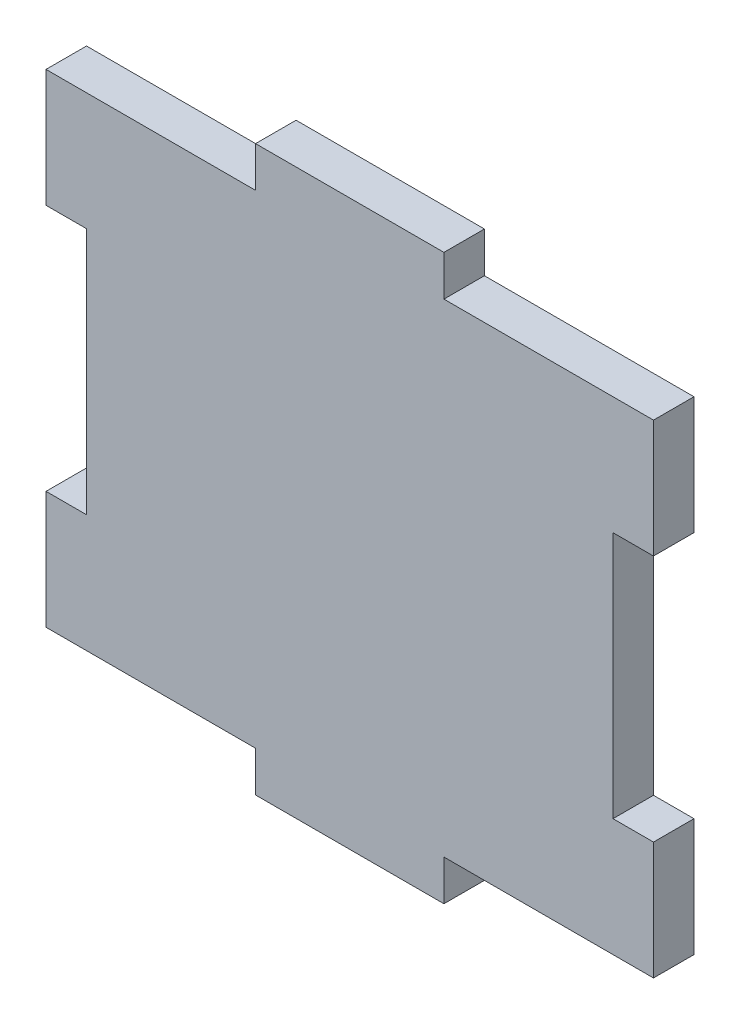
SolidWorks part; units mm, degrees
ref_plane "Front Plane" through (0, 0, 0) normal (0, 0, 1) x (1, 0, 0)
ref_plane "Top Plane" through (0, 0, 0) normal (0, 1, 0) x (1, 0, 0)
ref_plane "Right Plane" through (0, 0, 0) normal (1, 0, 0) x (0, 0, -1)
sketch "Sketch1" plane through (0, 0, 0) normal (0, 0, 1) x (1, 0, 0)
  line L1 (-40.9575, 32.5755) -> (40.9575, 32.5755)
  line L2 (-40.9575, 32.5755) -> (-40.9575, -32.5755)
  line L3 (-40.9575, -32.5755) -> (40.9575, -32.5755)
  line L4 (40.9575, 32.5755) -> (40.9575, -32.5755)
  line L5 (-40.9575, 32.5755) -> (40.9575, -32.5755) construction
  line L6 (-40.9575, -32.5755) -> (40.9575, 32.5755) construction
  point P0 (0, 0)
  dimension "D1" = 65.151
  dimension "D2" = 81.915
extrude "Boss-Extrude1" add sketch "Sketch1" along normal blind 5.461
sketch "Sketch2" plane through (0, 0, 5.461) normal (0, 0, 1) x (1, 0, 0)
  line L0 (-40.9575, 32.5755) -> (-40.9575, -32.5755) construction
  line L1 (-35.4965, 16.7005) -> (-40.9575, 16.7005)
  line L2 (-35.4965, 16.7005) -> (-35.4965, -16.7005)
  line L3 (-35.4965, -16.7005) -> (-40.9575, -16.7005)
  line L4 (-40.9575, 16.7005) -> (-40.9575, -16.7005)
  line L5 (-35.4965, 16.7005) -> (-40.9575, -16.7005) construction
  line L6 (-35.4965, -16.7005) -> (-40.9575, 16.7005) construction
  line L7 (40.9575, -32.5755) -> (40.9575, 32.5755) construction
  line L8 (35.4965, 16.7005) -> (40.9575, 16.7005)
  line L9 (35.4965, 16.7005) -> (35.4965, -16.7005)
  line L10 (35.4965, -16.7005) -> (40.9575, -16.7005)
  line L11 (40.9575, 16.7005) -> (40.9575, -16.7005)
  line L12 (35.4965, 16.7005) -> (40.9575, -16.7005) construction
  line L13 (35.4965, -16.7005) -> (40.9575, 16.7005) construction
  line L14 (40.9575, 32.5755) -> (-40.9575, 32.5755) construction
  point P0 (-38.227, 0)
  point P7 (38.227, 0)
  dimension "D1" = 15.875
  dimension "D2" = 5.461
extrude "Cut-Extrude1" cut sketch "Sketch2" against normal through all
sketch "Sketch3" plane through (0, 0, 0) normal (0, 0, 1) x (1, 0, 0)
  line L1 (-6.3509, -30.0355) -> (6.3509, -30.0355)
  line L2 (6.3509, -30.0355) -> (12.7017, -19.0355)
  line L3 (12.7017, -19.0355) -> (6.3509, -8.0355)
  line L4 (6.3509, -8.0355) -> (-6.3509, -8.0355)
  line L5 (-6.3509, -8.0355) -> (-12.7017, -19.0355)
  line L6 (-12.7017, -19.0355) -> (-6.3509, -30.0355)
  line L7 (-40.9575, -32.5755) -> (40.9575, -32.5755) construction
  circle A0 centre (0, -19.0355) radius 7.7
  circle A1 centre (0, -19.0355) radius 11 construction
  dimension "D2" = 15.4
  dimension "D1" = 22
  dimension "D4" = 2.54
extrude "Cut-Extrude2" [suppressed] cut sketch "Sketch3" along normal blind 2.54
sketch "Sketch4" plane through (0, 0, 5.461) normal (0, 0, 1) x (1, 0, 0)
  line L12 (-35.4965, 16.7005) -> (-35.4965, -16.7005)
  line L13 (-35.4965, 16.7005) -> (-35.4965, -16.7005)
  line L14 (-40.9575, 16.7005) -> (-35.4965, 16.7005)
  line L15 (-40.9575, 16.7005) -> (-35.4965, 16.7005)
  line L16 (-40.9575, 32.5755) -> (-40.9575, 16.7005)
  line L17 (-40.9575, 32.5755) -> (-40.9575, 16.7005)
  line L18 (40.9575, 32.5755) -> (-40.9575, 32.5755)
  line L19 (40.9575, 32.5755) -> (-40.9575, 32.5755)
  line L20 (40.9575, 16.7005) -> (40.9575, 32.5755)
  line L21 (40.9575, 16.7005) -> (40.9575, 32.5755)
  line L22 (35.4965, 16.7005) -> (40.9575, 16.7005)
  line L23 (35.4965, 16.7005) -> (40.9575, 16.7005)
  line L24 (35.4965, -16.7005) -> (35.4965, 16.7005)
  line L25 (35.4965, -16.7005) -> (35.4965, 16.7005)
  line L26 (40.9575, -16.7005) -> (35.4965, -16.7005)
  line L27 (40.9575, -16.7005) -> (35.4965, -16.7005)
  line L28 (40.9575, -32.5755) -> (40.9575, -16.7005)
  line L29 (40.9575, -32.5755) -> (40.9575, -16.7005)
  line L30 (-40.9575, -32.5755) -> (40.9575, -32.5755)
  line L31 (-40.9575, -32.5755) -> (40.9575, -32.5755)
  line L32 (-40.9575, -16.7005) -> (-40.9575, -32.5755)
  line L33 (-40.9575, -16.7005) -> (-40.9575, -32.5755)
  line L34 (-35.4965, -16.7005) -> (-40.9575, -16.7005)
  line L35 (-35.4965, -16.7005) -> (-40.9575, -16.7005)
  dimension "D1" = 0
extrude "Cut-Extrude3" [suppressed] cut sketch "Sketch4" against normal through all
sketch "Sketch5" plane through (0, 0, 0) normal (0, 0, -1) x (-1, 0, 0)
  line L0 (-40.9575, 32.5755) -> (40.9575, 32.5755) construction
  line L1 (12.7, 38.0365) -> (-12.7, 38.0365)
  line L2 (12.7, 38.0365) -> (12.7, 32.5755)
  line L3 (12.7, 32.5755) -> (-12.7, 32.5755)
  line L4 (-12.7, 38.0365) -> (-12.7, 32.5755)
  line L5 (12.7, 38.0365) -> (-12.7, 32.5755) construction
  line L6 (12.7, 32.5755) -> (-12.7, 38.0365) construction
  line L7 (40.9575, -32.5755) -> (-40.9575, -32.5755) construction
  line L8 (12.7, -38.0365) -> (-12.7, -38.0365)
  line L9 (12.7, -38.0365) -> (12.7, -32.5755)
  line L10 (12.7, -32.5755) -> (-12.7, -32.5755)
  line L11 (-12.7, -38.0365) -> (-12.7, -32.5755)
  line L12 (12.7, -38.0365) -> (-12.7, -32.5755) construction
  line L13 (12.7, -32.5755) -> (-12.7, -38.0365) construction
  point P0 (0, 35.306)
  point P7 (0, -35.306)
  point P14 (0, 0)
  dimension "D1" = 5.461
  dimension "D2" = 25.4
extrude "Boss-Extrude2" add sketch "Sketch5" against normal up to surface (5.461 mm away) up to face at (0, 0, 5.461)
equation "\"D1@Sketch1\"=1.85+.215+.5"
